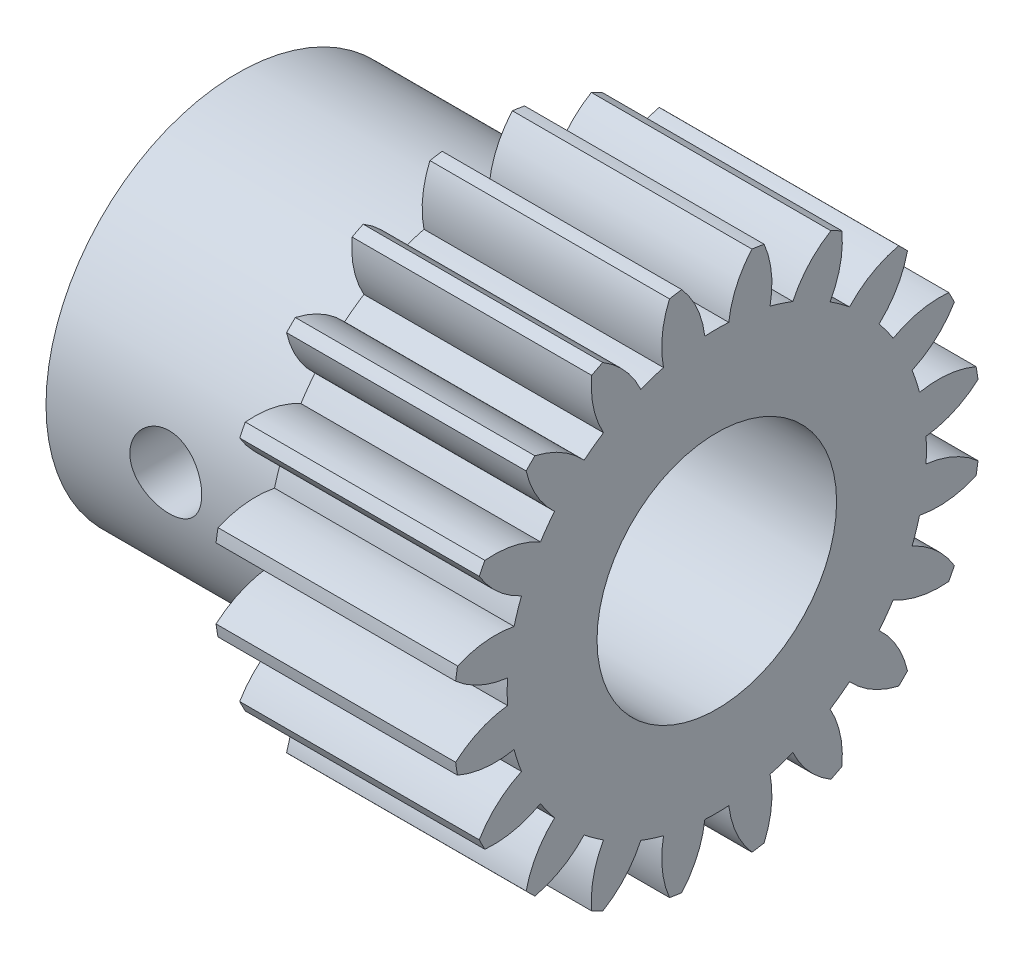
SolidWorks part; units mm, degrees
ref_plane "Plane1" through (0, 0, 0) normal (0, 0, 1) x (1, 0, 0)
ref_plane "Plane2" through (0, 0, 0) normal (0, 1, 0) x (1, 0, 0)
ref_plane "Plane3" through (0, 0, 0) normal (1, 0, 0) x (0, 0, -1)
other "Configuration Table"
sketch "HoldingSke" plane through (0, 0, 0) normal (0, 1, 0) x (1, 0, 0)
  line L0 (0, 0) -> (0.9397, -0.342)
  line L1 (-15, 0) -> (100, 0) construction
  line L2 (0, 0) -> (-2.1039, 2.3779)
  line L3 (0, 0) -> (-11.863, 4.5341)
  line L4 (0, 0) -> (8.1152, 2.9537)
  line L5 (0, 0) -> (-18.7391, -6.9891)
  line L6 (0, 0) -> (-8.2896, -5.593)
  line L7 (-2.1039, 2.3779) -> (2.2011, 21.9091)
  line L8 (-76.2, 54.61) -> (-74.4, 54.61)
  line L9 (-71.009, 38.7566) -> (-53.1078, 45.2721)
  line L10 (-76.2, 71.12) -> (104.1128, 71.12)
  line L11 (0, 0) -> (-10, 0)
  line L12 (-76.2, 101.6) -> (-76.162, 101.6)
  line L13 (24.9733, 27.94) -> (52.9518, 28.4284)
  line L14 (24.9733, 27.94) -> (24.9743, 27.94)
  line L15 (24.9733, 27.94) -> (100.4006, 29.5858)
  line L16 (-63.627, -1) -> (-12.827, -1)
  circle A0 centre (0, 0) radius 5
  circle A1 centre (0, 0) radius 8
  circle A2 centre (0, 0) radius 8
  circle A3 centre (0, 0) radius 5
  dimension "MHD" = 16
  dimension "Hub_dia" = 16
  dimension "Bore" = 10
  dimension "MBD" = 10
  dimension "Num_teeth" = 20
  dimension "Pitch" = 1
  dimension "Overall_len" = 20
  dimension "Show_teeth" = 20
  dimension "Thickness" = 10
  dimension "OAL" = 20.0001
  dimension "T_dim" = 1.8
  dimension "Ap" = 20
  dimension "H" = 19.05
  dimension "Pitch_radius" = 180.3128
  dimension "Width" = 10
  dimension "Backlash" = 0.038
  dimension "Addendum_fac" = 1
  dimension "Dedendum_fac" = 1.25
  dimension "Clearance_fac" = 0.25
  dimension "Dedendum_add" = 0.001
  dimension "Module" = 1
sketch "BasProSke" plane through (0, 0, 0) normal (0, 1, 0) x (1, 0, 0)
  line L0 (-10, 0) -> (60, 0) construction
  line L1 (0, 0) -> (0, 11)
  line L2 (0, 0) -> (10, 0)
  line L3 (10, 0) -> (10, 11)
  line L4 (10, 11) -> (0, 11)
  dimension "Thickness" = 10
  dimension "Diameter" = 22
revolve "Base-Revolve" add sketch "BasProSke" angle 360 about L0
sketch "TooCutSke" plane through (0, 0, 0) normal (1, 0, 0) x (0, 0, -1)
  line L1 (0, 0) -> (0, 107) construction
  line L2 (0, 0) -> (-0.8511, 9.9637) construction
  line L3 (0, 0) -> (-3.1206, 19.7028) construction
  line L4 (-0.8511, 9.9637) -> (-1.5603, 9.8514) construction
  arc A0 (0.4999, 8.7347) -> (-0.4999, 8.7347) centre (0, 0) ccw
  arc A1 (1.4852, 10.9249) -> (-1.4852, 10.9249) centre (0, 0) ccw
  circle A2 centre (0, 0) radius 10 construction
  circle A3 centre (0, 0) radius 9.3969 construction
  arc A4 (-0.4999, 8.7347) -> (-1.4852, 10.9249) centre (-4.4722, 8.2645) ccw
  arc A5 (1.4852, 10.9249) -> (0.4999, 8.7347) centre (4.4722, 8.2645) ccw
  dimension "Root_dia" = 17.498
  dimension "Overcut_dia" = 22.0508
  dimension "Pitch_dia" = 20
  dimension "Base_dia" = 18.7939
  dimension "Flank_rad" = 4
  dimension "Half_ang" = 9
  dimension "Half_CT" = 0.7181
extrude "ToothCut" cut sketch "TooCutSke" along normal through all
fillet "Breaks" [suppressed] radius 0.02
fillet "RootFillets" [suppressed] radius 0.251
pattern_circular "TeethCuts" count 20 every 18 about axis through (-10, 0, 0) along (1, 0, 0) of "ToothCut", "RootFillets", "Breaks"
sketch "HubNeaOneSke" plane through (0, 0, 0) normal (-1, 0, 0) x (0, 0, 1)
  circle A0 centre (0, 0) radius 8
  dimension "Diameter" = 16
extrude "HubNearOne" add sketch "HubNeaOneSke" along normal blind 10.0001
sketch "HubNeaBotSke" plane through (0, 0, 0) normal (-1, 0, 0) x (0, 0, 1)
  circle A0 centre (0, 0) radius 8
  dimension "Diameter" = 16
extrude "HubNearBoth" [suppressed] add sketch "HubNeaBotSke" along normal blind 5
ref_plane "FarPln" through (10, 0, 0) normal (1, 0, 0) x (0, 0, -1)
sketch "HubFarSke" plane through (10, 0, 0) normal (1, 0, 0) x (0, 0, -1)
  circle A0 centre (0, 0) radius 8
  dimension "Diameter" = 16
extrude "HubFar" [suppressed] add sketch "HubFarSke" along normal blind 5
sketch "BorSke" plane through (0, 0, 0) normal (1, 0, 0) x (0, 0, -1)
  circle A0 centre (0, 0) radius 5
  dimension "Diameter" = 10
extrude "Bore" cut sketch "BorSke" along normal mid plane 40.0001
sketch "KeySke" plane through (0, 0, 0) normal (1, 0, 0) x (0, 0, -1)
  line L0 (-2, 0) -> (-2, 6.8)
  line L1 (-2, 6.8) -> (2, 6.8)
  line L2 (2, 6.8) -> (2, 0)
  line L3 (0, 0) -> (0, 34) construction
  line L4 (-2, 0) -> (2, 0)
  dimension "Offset" = 6.8
  dimension "Width" = 4
extrude "Keyway" [suppressed] cut sketch "KeySke" along normal mid plane 40.0001
pattern_circular "Keyway2" [suppressed] count 2 every 90 about axis through (-10, 0, 0) along (1, 0, 0)
sketch "草图1" plane through (0, 0, 0) normal (0, 0, 1) x (1, 0, 0)
  line L0 (-10.0001, 8) -> (-10.0001, -8) construction
  circle A0 centre (-5.0001, 0) radius 1.5
  dimension "D1" = 3
  dimension "D2" = 5
extrude "切除-拉伸1" cut sketch "草图1" against normal blind 1 and the other way blind 9
equation "' \"Module@HoldingSke\" = 6.35"
equation "' \"Num_teeth@HoldingSke\" = 12"
equation "' \"Ap@HoldingSke\" =  20"
equation "' \"Ap@HoldingSke\" = 20"
equation "' \"Width@HoldingSke\" = 0.5 * 25.4"
equation "' \"Hub_dia@HoldingSke\"= 1 * 25.4"
equation "' \"Hub_dia@HoldingSke\" = 1 * 25.4"
equation "' \"Overall_len@HoldingSke\" = 1.0 * 25.4"
equation "' \"Bore@HoldingSke\" = 0.75 * 25.4"
equation "' \"T_dim@HoldingSke\" = 0.1 * 25.4"
equation "' \"Width@KeySke\" = 0.25 * 25.4"
equation "' \"Show_teeth@HoldingSke\" = 13"
equation "' \"Backlash@HoldingSke\" = 0.009 * 25.4"
equation "' \"Addendum_fac@HoldingSke\" = 1.0"
equation "' \"Dedendum_fac@HoldingSke\" = 1.25"
equation "' \"Dedendum_add@HoldingSke\" = 0.00005 * 25.4"
equation "' \"Clearance_fac@HoldingSke\" = 0.25"
equation "\"Pitch@HoldingSke\" = 1 / \"Module@HoldingSke\""
equation "\"Overcut_dia@TooCutSke\" = (\"Num_teeth@HoldingSke\" + 2 * \"Addendum_fac@HoldingSke\") / \"Pitch@HoldingSke\" + 0.002 * 25.4"
equation "\"Pitch_dia@TooCutSke\" = \"Num_teeth@HoldingSke\" / \"Pitch@HoldingSke\""
equation "\"Base_dia@TooCutSke\" = \"Num_teeth@HoldingSke\" / \"Pitch@HoldingSke\" * cos((\"Ap@HoldingSke\"  * 3.14159265 / 180))"
equation "\"Root_dia@TooCutSke\" = (\"Num_teeth@HoldingSke\" + 2) / \"Pitch@HoldingSke\" - 2 * (\"Addendum_fac@HoldingSke\" + \"Dedendum_fac@HoldingSke\") / \"Pitch@HoldingSke\" - \"Dedendum_add@HoldingSke\" * 2"
equation "\"Half_ang@TooCutSke\" = 180 / \"Num_teeth@HoldingSke\""
equation "\"Half_CT@TooCutSke\" = \"Num_teeth@HoldingSke\" / \"Pitch@HoldingSke\" * sin((3.14159265 / 2 / \"Num_teeth@HoldingSke\")) / 2 - 7 * \"Backlash@HoldingSke\" / 4"
equation "\"Flank_rad@TooCutSke\" = \"Num_teeth@HoldingSke\" / \"Pitch@HoldingSke\" / 5"
equation "\"Radius@RootFillets\" = \"Clearance_fac@HoldingSke\" / \"Pitch@HoldingSke\" + \"Dedendum_add@HoldingSke\""
equation "\"Break_rad@Breaks\" = 0.02 / \"Pitch@HoldingSke\""
equation "\"Thickness@HoldingSke\" = \"Width@HoldingSke\""
equation "\"OAL@HoldingSke\" = \"Thickness@HoldingSke\""
equation "\"MHD@HoldingSke\" = (\"Num_teeth@HoldingSke\" + 2) / \"Pitch@HoldingSke\" - 2 * (\"Addendum_fac@HoldingSke\" + \"Dedendum_fac@HoldingSke\")  / \"Pitch@HoldingSke\" - \"Dedendum_add@HoldingSke\" * 2"
equation "\"MBD@HoldingSke\" = (\"Num_teeth@HoldingSke\" + 2) / \"Pitch@HoldingSke\" - 2 * (\"Addendum_fac@HoldingSke\" + \"Dedendum_fac@HoldingSke\")  / \"Pitch@HoldingSke\" - \"Dedendum_add@HoldingSke\" * 2 - 0.002 * 25.4"
equation "\"MHD@HoldingSke\" = ((sgn( \"MHD@HoldingSke\" - \"Hub_dia@HoldingSke\" )-1)*( \"MHD@HoldingSke\" - \"Hub_dia@HoldingSke\" ))/-2+ \"Hub_dia@HoldingSke\""
equation "\"MBD@HoldingSke\" = ((sgn( \"MBD@HoldingSke\" - \"Bore@HoldingSke\" )-1)*( \"MBD@HoldingSke\" - \"Bore@HoldingSke\" ))/-2+ \"Bore@HoldingSke\""
equation "\"OAL@HoldingSke\" = ((sgn( \"OAL@HoldingSke\" - \"Overall_len@HoldingSke\" )+1)*( \"OAL@HoldingSke\" - \"Overall_len@HoldingSke\" ))/2 + \"Overall_len@HoldingSke\" + 0.000002 * 25.4"
equation "\"Num_teeth@TeethCuts\" = int( \"Show_teeth@HoldingSke\" ) + 1"
equation "\"Num_teeth@TeethCuts\" = ((sgn( \"Num_teeth@TeethCuts\" - \"Num_teeth@HoldingSke\" )-1)*( \"Num_teeth@TeethCuts\" - \"Num_teeth@HoldingSke\" ))/-2+ \"Num_teeth@HoldingSke\""
equation "\"Num_teeth@TeethCuts\" = ((sgn( \"Num_teeth@TeethCuts\" - 2.0)+1)*( \"Num_teeth@TeethCuts\" - 2.0))/2 +2.0"
equation "\"Angle@TeethCuts\" = 360.0 / \"Num_teeth@HoldingSke\""
equation "\"Diameter@BasProSke\" = (\"Num_teeth@HoldingSke\" + 2 * \"Addendum_fac@HoldingSke\") / \"Pitch@HoldingSke\""
equation "\"Thickness@BasProSke\"  = \"Thickness@HoldingSke\""
equation "' \"Fillet_rad@BasProSke\" =  \"Thickness@HoldingSke\" * 0.05"
equation "' \"Fillet_rad@BasProSke\" = \"Thickness@HoldingSke\" * 0.05"
equation "\"MHD@HoldingSke\" = ((sgn( \"MHD@HoldingSke\" - \"Root_dia@TooCutSke\" )-1)*( \"MHD@HoldingSke\" - \"Root_dia@TooCutSke\" ))/-2+ \"Root_dia@TooCutSke\""
equation "\"Diameter@HubNeaOneSke\" = \"MHD@HoldingSke\""
equation "\"Length@HubNearOne\" = \"OAL@HoldingSke\" - \"Thickness@BasProSke\""
equation "\"Diameter@HubNeaBotSke\" = \"MHD@HoldingSke\""
equation "\"Length@HubNearBoth\" = ( \"OAL@HoldingSke\" - \"Thickness@BasProSke\" ) / 2.0"
equation "\"Thickness@FarPln\" = \"Thickness@BasProSke\""
equation "\"Diameter@HubFarSke\" = \"MHD@HoldingSke\""
equation "\"Length@HubFar\" = ( \"OAL@HoldingSke\" - \"Thickness@BasProSke\" ) / 2.0"
equation "\"Diameter@BorSke\" = \"MBD@HoldingSke\""
equation "\"D1@Bore\" = \"OAL@HoldingSke\" * 2.0"
equation "\"D1@Keyway\" = \"OAL@HoldingSke\" * 2.0"
equation "\"Offset@KeySke\" = \"T_dim@HoldingSke\" + \"MBD@HoldingSke\" / 2.0"
